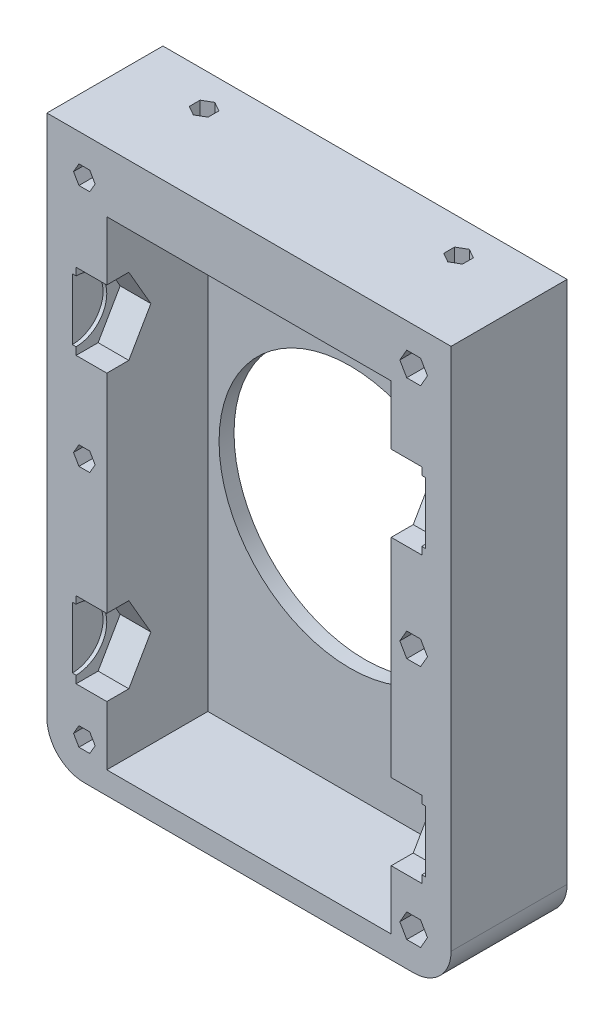
SolidWorks part; units mm, degrees
ref_plane "Front Plane" through (0, 0, 0) normal (0, 0, 1) x (1, 0, 0)
ref_plane "Top Plane" through (0, 0, 0) normal (0, 1, 0) x (1, 0, 0)
ref_plane "Right Plane" through (0, 0, 0) normal (1, 0, 0) x (0, 0, -1)
sketch "Sketch1" plane through (0, 0, 0) normal (0, 0, 1) x (1, 0, 0)
  line L1 (0, 0) -> (54, 0)
  line L2 (0, 0) -> (0, 75)
  line L3 (0, 75) -> (54, 75)
  line L4 (54, 0) -> (54, 75)
  line L5 (8, 67) -> (46, 67)
  line L6 (8, 67) -> (8, 3)
  line L7 (8, 3) -> (46, 3)
  line L8 (46, 67) -> (46, 3)
  dimension "D1" = 75
  dimension "D2" = 54
  dimension "D3" = 8
  dimension "D4" = 8
  dimension "D5" = 3
  dimension "D6" = 8
extrude "Boss-Extrude1" add sketch "Sketch1" along normal blind 27
sketch "Sketch2" plane through (46, 0, 0) normal (-1, 0, 0) x (0, 0, 1)
  line L0 (13.5, 67) -> (13.5, 3) construction
  line L1 (19.389, 54) -> (16.4445, 59.1)
  line L2 (16.4445, 59.1) -> (10.5555, 59.1)
  line L3 (10.5555, 59.1) -> (7.611, 54)
  line L4 (7.611, 54) -> (10.5555, 48.9)
  line L5 (10.5555, 48.9) -> (16.4445, 48.9)
  line L6 (16.4445, 48.9) -> (19.389, 54)
  line L8 (0, 3) -> (0, 67) construction
  line L10 (19.389, 16) -> (16.4445, 21.1)
  line L11 (16.4445, 21.1) -> (10.5555, 21.1)
  line L12 (10.5555, 21.1) -> (7.611, 16)
  line L13 (7.611, 16) -> (10.5555, 10.9)
  line L14 (10.5555, 10.9) -> (16.4445, 10.9)
  line L15 (16.4445, 10.9) -> (19.389, 16)
  line L16 (10.5555, 59.1) -> (16.4445, 48.9) construction
  line L17 (16.4445, 10.9) -> (10.5555, 21.1) construction
  line L18 (10.5555, 48.9) -> (16.4445, 59.1) construction
  line L19 (27, 67) -> (0, 67) construction
  line L20 (27, 3) -> (0, 3) construction
  line L21 (0, 35) -> (27, 35) construction
  line L22 (27, 3) -> (27, 67) construction
  line L23 (16.4445, 21.1) -> (10.5555, 10.9) construction
  circle A0 centre (13.5, 54) radius 5.1 construction
  circle A1 centre (13.5, 16) radius 5.1 construction
  point P28 (13.5, 35)
  dimension "D1" = 19
  dimension "D2" = 13.5
  dimension "D3" = 10.2
  dimension "D4" = 19
  dimension "D5" = 13.5
  dimension "D6" = 10.2
extrude "Cut-Extrude1" cut sketch "Sketch2" against normal blind 4.1
sketch "Sketch5" plane through (50.1, 0, 0) normal (-1, 0, 0) x (0, 0, 1)
  line L0 (10.5555, 59.1) -> (16.4445, 48.9) construction
  line L1 (10.5555, 48.9) -> (16.4445, 59.1) construction
  line L2 (10.5555, 10.9) -> (16.4445, 21.1) construction
  line L3 (16.4445, 10.9) -> (10.5555, 21.1) construction
  circle A0 centre (13.5, 54) radius 4.1
  circle A1 centre (13.5, 16) radius 4.1
  dimension "D1" = 8.2
  dimension "D2" = 8.2
extrude "Cut-Extrude2" cut sketch "Sketch5" against normal blind 0.5
sketch "Sketch6" plane through (8, 0, 0) normal (1, 0, 0) x (0, 0, -1)
  line L1 (-7.611, 54) -> (-10.5555, 59.1)
  line L2 (-10.5555, 59.1) -> (-16.4445, 59.1)
  line L3 (-16.4445, 59.1) -> (-19.389, 54)
  line L4 (-19.389, 54) -> (-16.4445, 48.9)
  line L5 (-16.4445, 48.9) -> (-10.5555, 48.9)
  line L6 (-10.5555, 48.9) -> (-7.611, 54)
  line L7 (-7.611, 16) -> (-10.5555, 21.1)
  line L8 (-10.5555, 21.1) -> (-16.4445, 21.1)
  line L9 (-16.4445, 21.1) -> (-19.389, 16)
  line L10 (-19.389, 16) -> (-16.4445, 10.9)
  line L11 (-16.4445, 10.9) -> (-10.5555, 10.9)
  line L12 (-10.5555, 10.9) -> (-7.611, 16)
  line L13 (-27, 67) -> (-27, 3) construction
  line L15 (-27, 35) -> (0, 35) construction
  line L16 (0, 67) -> (0, 3) construction
  circle A0 centre (-13.5, 54) radius 5.1 construction
  circle A1 centre (-13.5, 16) radius 5.1 construction
  dimension "D1" = 19
  dimension "D2" = 13.5
  dimension "D3" = 19
  dimension "D4" = 13.5
  dimension "D5" = 10.2
  dimension "D6" = 10.2
extrude "Cut-Extrude3" cut sketch "Sketch6" against normal blind 4.1
sketch "Sketch7" plane through (3.9, 0, 0) normal (1, 0, 0) x (0, 0, -1)
  line L0 (-10.5555, 21.1) -> (-16.4445, 10.9) construction
  line L3 (-10.5555, 59.1) -> (-16.4445, 48.9) construction
  circle A0 centre (-13.5, 54) radius 4.1
  circle A1 centre (-13.5, 16) radius 4.1
  point P16 (-13.5, 54)
  point P17 (-13.5, 16)
  dimension "D1" = 8.2
  dimension "D5" = 0
extrude "Cut-Extrude4" cut sketch "Sketch7" against normal blind 0.5
sketch "Sketch8" plane through (0, 0, 27) normal (0, 0, 1) x (1, 0, 0)
  line L1 (0, 75) -> (54, 75)
  line L2 (0, 75) -> (0, 0)
  line L3 (0, 0) -> (54, 0)
  line L4 (54, 75) -> (54, 0)
extrude "Boss-Extrude2" add sketch "Sketch8" along normal blind 2
sketch "Sketch9" plane through (0, 0, 0) normal (0, 0, -1) x (-1, 0, 0)
  line L1 (-54, 75) -> (0, 75)
  line L2 (-54, 75) -> (-54, 0)
  line L3 (-54, 0) -> (0, 0)
  line L4 (0, 75) -> (0, 0)
extrude "Boss-Extrude3" add sketch "Sketch9" along normal blind 2
sketch "Sketch10" plane through (0, 0, 29) normal (0, 0, 1) x (1, 0, 0)
  line L1 (0, 75) -> (54, 75)
  line L2 (0, 75) -> (0, 0)
  line L3 (0, 0) -> (54, 0)
  line L4 (54, 75) -> (54, 0)
extrude "Cut-Extrude5" cut sketch "Sketch10" against normal blind 15.5
sketch "Sketch11" plane through (0, 0, 0) normal (0, 0, 1) x (1, 0, 0)
  line L1 (0, 75) -> (54, 75) construction
  line L2 (54, 75) -> (54, 0) construction
  circle A0 centre (27, 35) radius 17.5
  point P6 (27, 35)
  dimension "D1" = 35
  dimension "D2" = 40
  dimension "D3" = 27
extrude "Cut-Extrude6" cut sketch "Sketch11" against normal through all
sketch "Sketch12" plane through (0, 0, 13.5) normal (0, 0, 1) x (1, 0, 0)
  line L0 (54, 0) -> (54, 75) construction
  line L1 (6.4434, 70) -> (5.7217, 71.25)
  line L2 (5.7217, 71.25) -> (4.2783, 71.25)
  line L3 (4.2783, 71.25) -> (3.5566, 70)
  line L4 (3.5566, 70) -> (4.2783, 68.75)
  line L5 (4.2783, 68.75) -> (5.7217, 68.75)
  line L6 (5.7217, 68.75) -> (6.4434, 70)
  line L7 (50.8475, 70) -> (49.9238, 71.6)
  line L8 (49.9238, 71.6) -> (48.0762, 71.6)
  line L9 (48.0762, 71.6) -> (47.1525, 70)
  line L10 (47.1525, 70) -> (48.0762, 68.4)
  line L11 (48.0762, 68.4) -> (49.9238, 68.4)
  line L12 (49.9238, 68.4) -> (50.8475, 70)
  line L13 (5, 70) -> (5, 5) construction
  line L14 (54, 75) -> (0, 75) construction
  line L15 (0, 75) -> (0, 0) construction
  line L16 (49, 70) -> (49, 5) construction
  line L17 (0, 0) -> (54, 0) construction
  line L19 (6.4434, 5) -> (5.7217, 6.25)
  line L20 (5.7217, 6.25) -> (4.2783, 6.25)
  line L21 (4.2783, 6.25) -> (3.5566, 5)
  line L22 (3.5566, 5) -> (4.2783, 3.75)
  line L23 (4.2783, 3.75) -> (5.7217, 3.75)
  line L24 (5.7217, 3.75) -> (6.4434, 5)
  line L25 (50.8475, 5) -> (49.9238, 6.6)
  line L26 (49.9238, 6.6) -> (48.0762, 6.6)
  line L27 (0, 37.5) -> (54, 37.5) construction
  line L28 (48.0762, 6.6) -> (47.1525, 5)
  line L29 (47.1525, 5) -> (48.0762, 3.4)
  line L30 (48.0762, 3.4) -> (49.9238, 3.4)
  line L31 (49.9238, 3.4) -> (50.8475, 5)
  line L32 (50.8475, 37.5) -> (49.9238, 39.1)
  line L33 (49.9238, 39.1) -> (48.0762, 39.1)
  line L34 (48.0762, 39.1) -> (47.1525, 37.5)
  line L35 (47.1525, 37.5) -> (48.0762, 35.9)
  line L36 (48.0762, 35.9) -> (49.9238, 35.9)
  line L37 (49.9238, 35.9) -> (50.8475, 37.5)
  line L38 (6.4434, 37.5) -> (5.7217, 38.75)
  line L39 (5.7217, 38.75) -> (4.2783, 38.75)
  line L40 (4.2783, 38.75) -> (3.5566, 37.5)
  line L41 (3.5566, 37.5) -> (4.2783, 36.25)
  line L42 (4.2783, 36.25) -> (5.7217, 36.25)
  line L43 (5.7217, 36.25) -> (6.4434, 37.5)
  circle A0 centre (5, 70) radius 1.25 construction
  circle A1 centre (49, 70) radius 1.6 construction
  circle A2 centre (5, 5) radius 1.25 construction
  circle A3 centre (49, 5) radius 1.6 construction
  circle A4 centre (49, 37.5) radius 1.6 construction
  circle A5 centre (5, 37.5) radius 1.25 construction
  dimension "D1" = 2.5
  dimension "D2" = 3.2
  dimension "D3" = 5
  dimension "D4" = 5
  dimension "D5" = 5
  dimension "D6" = 5
  dimension "D7" = 5
extrude "Cut-Extrude7" cut sketch "Sketch12" against normal through all
sketch "Sketch14" plane through (0, 67, 0) normal (0, -1, 0) x (1, 0, 0)
  line L0 (46, 13.5) -> (46, 0) construction
  line L1 (8, 0) -> (46, 0)
  line L2 (8, 0) -> (8, 5)
  line L3 (8, 5) -> (46, 5)
  line L4 (46, 0) -> (46, 5)
  dimension "D1" = 5
extrude "Boss-Extrude4" add sketch "Sketch14" along normal blind 4
sketch "Sketch13" plane through (0, 75, 0) normal (0, 1, 0) x (1, 0, 0)
  line L0 (54, -13.5) -> (0, -13.5) construction
  line L1 (44, -1.0566) -> (42.75, -1.7783)
  line L2 (42.75, -1.7783) -> (42.75, -3.2217)
  line L3 (42.75, -3.2217) -> (44, -3.9434)
  line L4 (44, -3.9434) -> (45.25, -3.2217)
  line L5 (45.25, -3.2217) -> (45.25, -1.7783)
  line L6 (45.25, -1.7783) -> (44, -1.0566)
  line L7 (10, -1.0566) -> (8.75, -1.7783)
  line L8 (8.75, -1.7783) -> (8.75, -3.2217)
  line L9 (8.75, -3.2217) -> (10, -3.9434)
  line L10 (10, -3.9434) -> (11.25, -3.2217)
  line L11 (11.25, -3.2217) -> (11.25, -1.7783)
  line L12 (11.25, -1.7783) -> (10, -1.0566)
  line L13 (54, -13.5) -> (54, 2) construction
  line L14 (0, -13.5) -> (0, 2) construction
  circle A0 centre (44, -2.5) radius 1.25 construction
  circle A1 centre (10, -2.5) radius 1.25 construction
  dimension "D1" = 11
  dimension "D2" = 11
  dimension "D3" = 10
  dimension "D4" = 10
  dimension "D5" = 2.5
  dimension "D6" = 2.5
extrude "Cut-Extrude8" cut sketch "Sketch13" against normal up to next
fillet "Fillet1" radius 5 2 edges at (54, 0, 5.75) (0, 0, 5.75)
